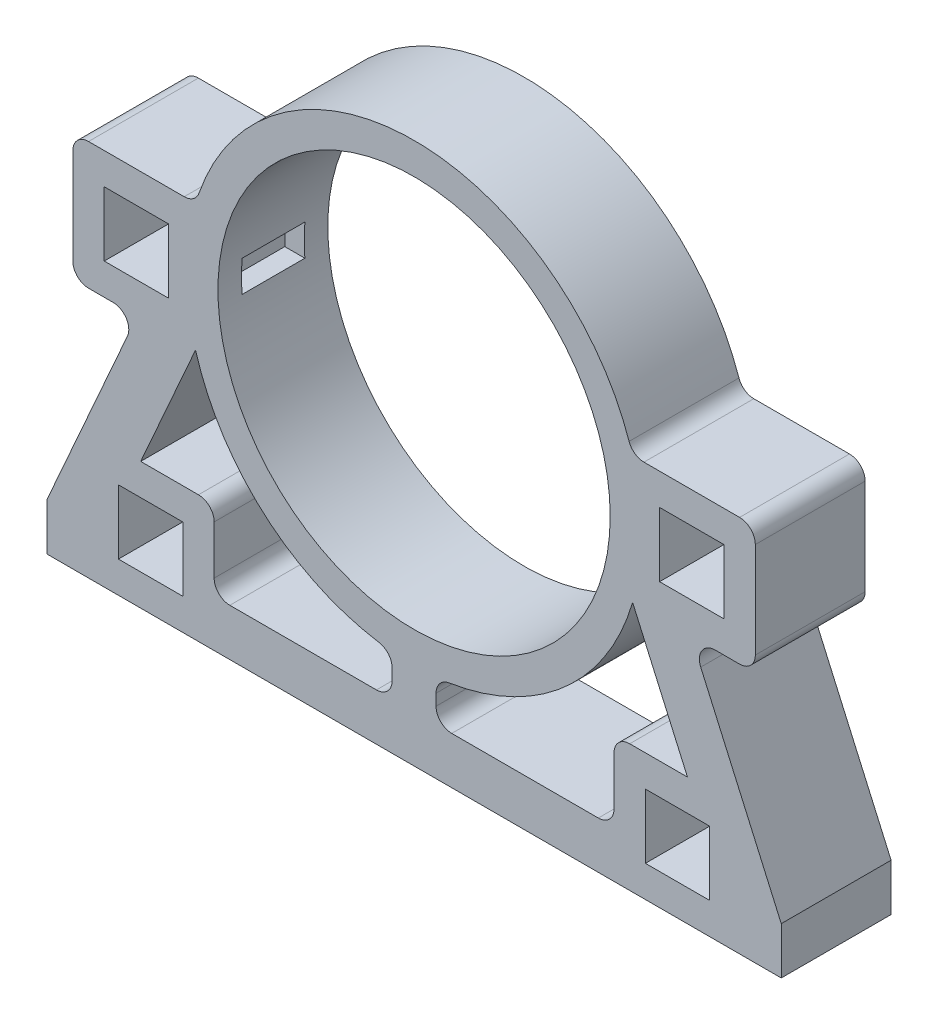
SolidWorks part; units mm, degrees
material "1023 Carbon Steel Sheet (SS)"
ref_plane "Ön Düzlem" through (0, 0, 0) normal (0, 0, 1) x (1, 0, 0)
ref_plane "Üst Düzlem" through (0, 0, 0) normal (0, 1, 0) x (1, 0, 0)
ref_plane "Sağ Düzlem" through (0, 0, 0) normal (1, 0, 0) x (0, 0, -1)
sketch "Sketch1" plane through (0, 0, 0) normal (0, 0, 1) x (1, 0, 0)
  line L0 (-7, -72.1613) -> (-7, -85.1613)
  line L1 (-7, -85.1613) -> (7, -85.1613)
  line L2 (94.2084, -90.1613) -> (73.7084, -69.6613) construction
  line L3 (94.2084, -69.6613) -> (73.7084, -90.1613) construction
  line L4 (-7, -85.1613) -> (-117, -85.1613)
  line L6 (-117, -85.1613) -> (-117, -100.1613)
  line L8 (-117, -100.1613) -> (117, -100.1613)
  line L13 (0, -100.1613) -> (0, -85.1613)
  line L14 (63.7084, -85.1613) -> (63.7084, -59.6613)
  line L15 (63.7084, -59.6613) -> (105.7084, -59.6613)
  line L16 (94.2084, -69.6613) -> (73.7084, -69.6613)
  line L17 (-117, -85.1613) -> (-66.2915, 29.3544)
  line L20 (-63.7084, -85.1613) -> (-63.7084, -59.6613)
  line L21 (-63.7084, -59.6613) -> (-105.7084, -59.6613)
  line L22 (-92.6994, -72.2698) -> (-69.6344, -20.1817)
  line L23 (94.2084, -90.1613) -> (94.2084, -69.6613)
  line L28 (-69.6344, -20.1817) -> (-108.7348, -20.1817)
  line L29 (-94.2084, -90.1613) -> (-73.7084, -90.1613)
  line L30 (94.2084, -90.1613) -> (73.7084, -90.1613)
  line L31 (73.7084, -90.1613) -> (73.7084, -69.6613)
  line L32 (7, -85.1613) -> (117, -85.1613)
  line L37 (7, -72.1613) -> (7, -85.1613)
  line L38 (117, -85.1613) -> (117, -100.1613)
  line L39 (-94.2084, -90.1613) -> (-94.2084, -69.6613)
  line L40 (-94.2084, -69.6613) -> (-73.7084, -69.6613)
  line L41 (-73.7084, -90.1613) -> (-73.7084, -69.6613)
  line L42 (-94.2084, -90.1613) -> (-73.7084, -69.6613) construction
  line L43 (-94.2084, -69.6613) -> (-73.7084, -90.1613) construction
  line L44 (-108.7348, -20.1817) -> (-108.7348, 20.3183)
  line L45 (-108.7348, 20.3183) -> (-69.5947, 20.3183)
  line L46 (0, -55) -> (0, 55) construction
  line L47 (-98.7348, -10.1817) -> (-78.2348, -10.1817)
  line L48 (-98.7348, -10.1817) -> (-98.7348, 10.3183)
  line L49 (-98.7348, 10.3183) -> (-78.2348, 10.3183)
  line L50 (-78.2348, -10.1817) -> (-78.2348, 10.3183)
  line L51 (-98.7348, -10.1817) -> (-78.2348, 10.3183) construction
  line L52 (-98.7348, 10.3183) -> (-78.2348, -10.1817) construction
  line L53 (98.7348, -10.1817) -> (78.2348, 10.3183) construction
  line L54 (98.7348, 10.3183) -> (78.2348, -10.1817) construction
  line L55 (108.7348, 20.3183) -> (69.5947, 20.3183)
  line L56 (108.7348, -20.1817) -> (108.7348, 20.3183)
  line L57 (98.7348, -10.1817) -> (98.7348, 10.3183)
  line L58 (69.6344, -20.1817) -> (108.7348, -20.1817)
  line L59 (78.2348, -10.1817) -> (78.2348, 10.3183)
  line L60 (78.2348, 10.3183) -> (98.7348, 10.3183)
  line L61 (98.7348, -10.1817) -> (78.2348, -10.1817)
  line L62 (117, -85.1613) -> (66.2915, 29.3544)
  line L63 (92.6994, -72.2698) -> (69.6344, -20.1817)
  circle A0 centre (0, 0) radius 62.5
  circle A1 centre (0, 0) radius 72.5
  point P9 (-94.2084, -79.9113)
  point P10 (83.9584, -79.9113)
  point P23 (0, 0)
  point P25 (-85, -85.1613)
  point P28 (-83.9584, -79.9113)
  point P38 (94.2084, -79.9113)
  point P43 (-88.4848, 0.0683)
  point P61 (0, 0)
  point P62 (0, 0)
  dimension "D1" = 125
  dimension "D2" = 10
  dimension "D6" = 10
  dimension "D7" = 17
  dimension "D11" = 20.5
  dimension "D3" = 15
  dimension "D4" = 13
  dimension "D5" = 110
  dimension "D8" = 25.5
  dimension "D9" = 10
  dimension "D10" = 20.5
  dimension "D13" = 100.1613
  dimension "D19" = 40.5
  dimension "D20" = 39.1401
  dimension "D21" = 20.5
  dimension "D22" = 20.5
  dimension "D23" = 10
  dimension "D24" = 10
  dimension "D25" = 42
ref_plane "Plane6" through (61.7, 0, 0) normal (1, 0, 0) x (0, 0, -1)
ref_plane "Plane7" through (-61.7, 0, 0) normal (1, 0, 0) x (0, 0, -1)
extrude "Boss-Extrude1" add sketch "Sketch1" along normal blind 35 contours A1 A0 | L50 L17 L45 L44 L28 L47 L48 L49 | A1 L45 L17 L50 L47 L28 | L22 L28 L17 L21 | L39 L40 L22 L21 L17 L4 | L41 L29 L39 L4 L6 L8 L13 L1 | L41 L4 L20 L21 L22 L40 | A1 L0 L1 L37 | L38 L32 L23 L30 L31 L1 L13 L8 | L16 L63 L15 L14 L32 L31 | L63 L16 L23 L32 L62 L15 | L63 L15 L62 L58 | A1 L58 L62 L61 L59 L55 | L62 L58 L56 L55 L59 L60 L57 L61
fillet "Fillet2" radius 5 16 edges at (-108.7348, 20.3183, 17.5) (-69.5947, 20.3183, 17.5) (-88.2265, -20.1817, 17.5) (-108.7348, -20.1817, 17.5) (-63.7084, -85.1613, 17.5) (-63.7084, -59.6613, 17.5) (7, -85.1613, 17.5) (7, -72.1613, 17.5) (-7, -85.1613, 17.5) (-7, -72.1613, 17.5) (63.7084, -85.1613, 17.5) (63.7084, -59.6613, 17.5) (88.2265, -20.1817, 17.5) (108.7348, -20.1817, 17.5) (69.5947, 20.3183, 17.5) (108.7348, 20.3183, 17.5)
sketch "Sketch2" plane through (61.7, 0, 0) normal (1, 0, 0) x (0, 0, -1)
  line L0 (-35, -10.1817) -> (0, -10.1817) construction
  line L1 (-7.5, -4.9317) -> (-27.5, -4.9317)
  line L2 (-7.5, -4.9317) -> (-7.5, 5.0683)
  line L3 (-7.5, 5.0683) -> (-27.5, 5.0683)
  line L4 (-27.5, -4.9317) -> (-27.5, 5.0683)
  line L5 (-7.5, -4.9317) -> (-27.5, 5.0683) construction
  line L6 (-7.5, 5.0683) -> (-27.5, -4.9317) construction
  line L7 (0, -10.1817) -> (0, 10.3183) construction
  point P0 (-17.5, 0.0683)
  dimension "D1" = 20
  dimension "D2" = 10
  dimension "D3" = 5.25
  dimension "D4" = 7.5
extrude "Cut-Extrude2" cut sketch "Sketch2" along normal blind 7
sketch "Sketch3" plane through (-61.7, 0, 0) normal (1, 0, 0) x (0, 0, -1)
  line L0 (0, -10.1817) -> (0, 10.3183) construction
  line L1 (-27.5, -4.9317) -> (-7.5, -4.9317)
  line L2 (-27.5, -4.9317) -> (-27.5, 5.0683)
  line L3 (-27.5, 5.0683) -> (-7.5, 5.0683)
  line L4 (-7.5, -4.9317) -> (-7.5, 5.0683)
  line L5 (-27.5, -4.9317) -> (-7.5, 5.0683) construction
  line L6 (-27.5, 5.0683) -> (-7.5, -4.9317) construction
  line L7 (-35, -10.1817) -> (0, -10.1817) construction
  point P0 (-17.5, 0.0683)
  dimension "D1" = 20
  dimension "D2" = 10
  dimension "D3" = 7.5
  dimension "D4" = 5.25
extrude "Cut-Extrude3" cut sketch "Sketch3" against normal blind 7
